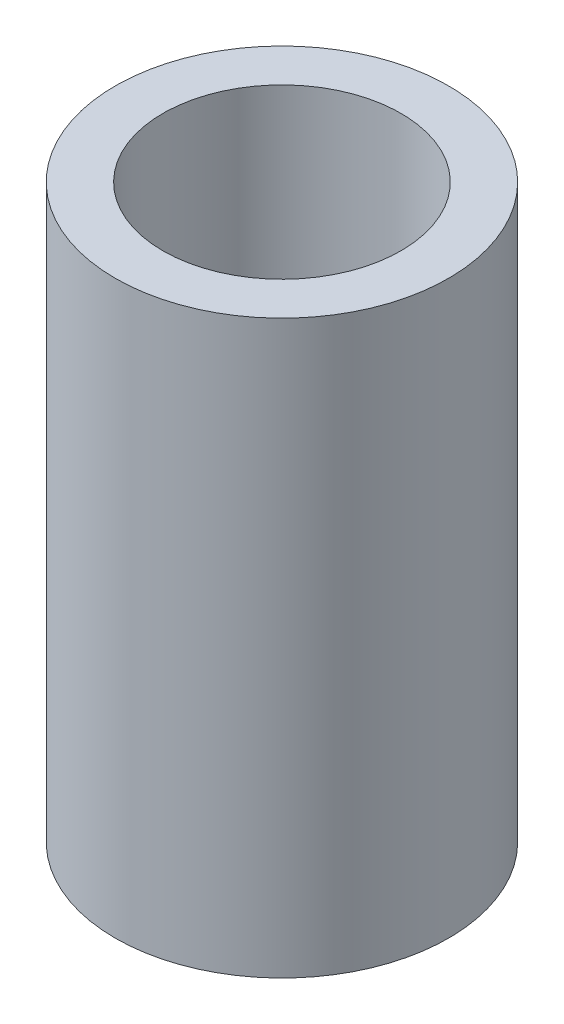
SolidWorks part; units mm, degrees
ref_plane "Front Plane" through (0, 0, 0) normal (0, 0, 1) x (1, 0, 0)
ref_plane "Top Plane" through (0, 0, 0) normal (0, 1, 0) x (1, 0, 0)
ref_plane "Right Plane" through (0, 0, 0) normal (1, 0, 0) x (0, 0, -1)
sketch "Sketch1" plane through (0, 0, 0) normal (0, 1, 0) x (1, 0, 0)
  circle A0 centre (0, 0) radius 7.9375
  circle A1 centre (0, 0) radius 11.1125
  dimension "D1" = 22.225
  dimension "D2" = 15.875
extrude "Boss-Extrude1" add sketch "Sketch1" along normal blind 38.1
